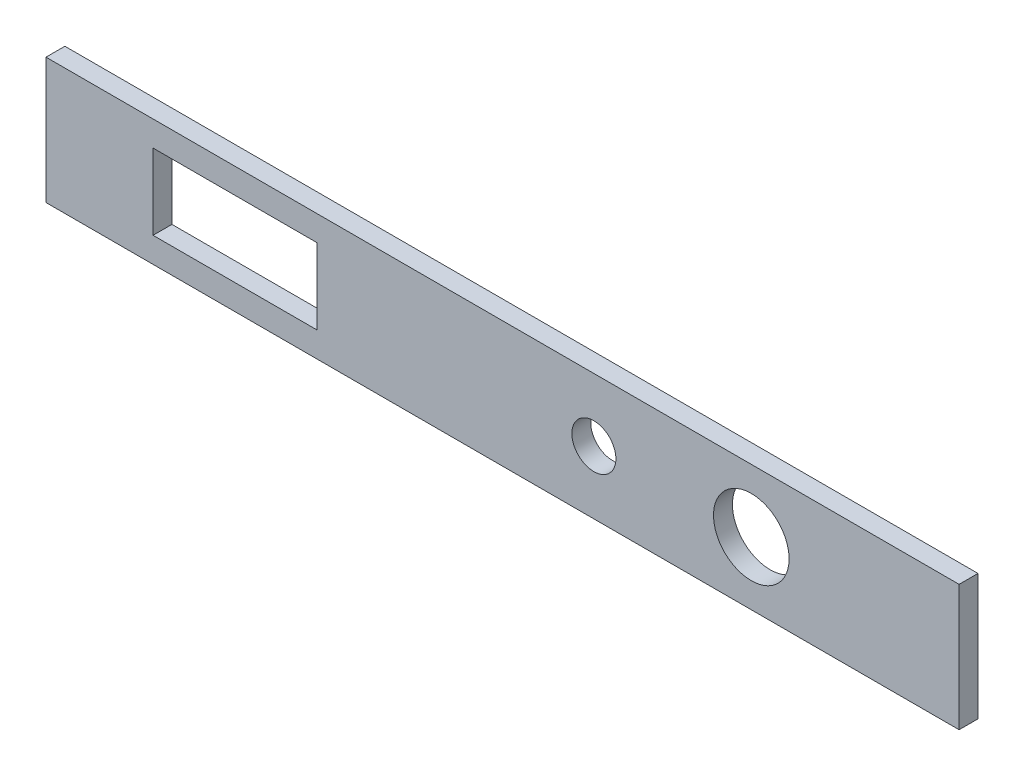
SolidWorks part; units mm, degrees
ref_plane "Front Plane" through (0, 0, 0) normal (0, 0, 1) x (1, 0, 0)
ref_plane "Top Plane" through (0, 0, 0) normal (0, 1, 0) x (1, 0, 0)
ref_plane "Right Plane" through (0, 0, 0) normal (1, 0, 0) x (0, 0, -1)
sketch "Sketch1" plane through (0, 0, 0) normal (0, 0, 1) x (1, 0, 0)
  line L1 (0, 0) -> (145, 0)
  line L2 (0, 0) -> (0, 20)
  line L3 (0, 20) -> (145, 20)
  line L4 (145, 0) -> (145, 20)
  dimension "D1" = 20
  dimension "D2" = 145
extrude "Boss-Extrude1" add sketch "Sketch1" along normal blind 3
sketch "Sketch2" plane through (0, 0, 3) normal (0, 0, 1) x (1, 0, 0)
  line L0 (0, 0) -> (145, 0) construction
  line L1 (17, 16) -> (43, 16)
  line L2 (17, 16) -> (17, 4)
  line L3 (17, 4) -> (43, 4)
  line L4 (43, 16) -> (43, 4)
  line L9 (145, 0) -> (145, 20) construction
  circle A0 centre (87, 10) radius 3.5
  circle A1 centre (112, 10) radius 6
  point P8 (17, 10)
  dimension "D1" = 12
  dimension "D2" = 7
  dimension "D6" = 10
  dimension "D3" = 26
  dimension "D4" = 12
  dimension "D5" = 10
  dimension "D7" = 10
  dimension "D8" = 33
  dimension "D9" = 58
  dimension "D10" = 102
extrude "Cut-Extrude1" cut sketch "Sketch2" against normal through all
